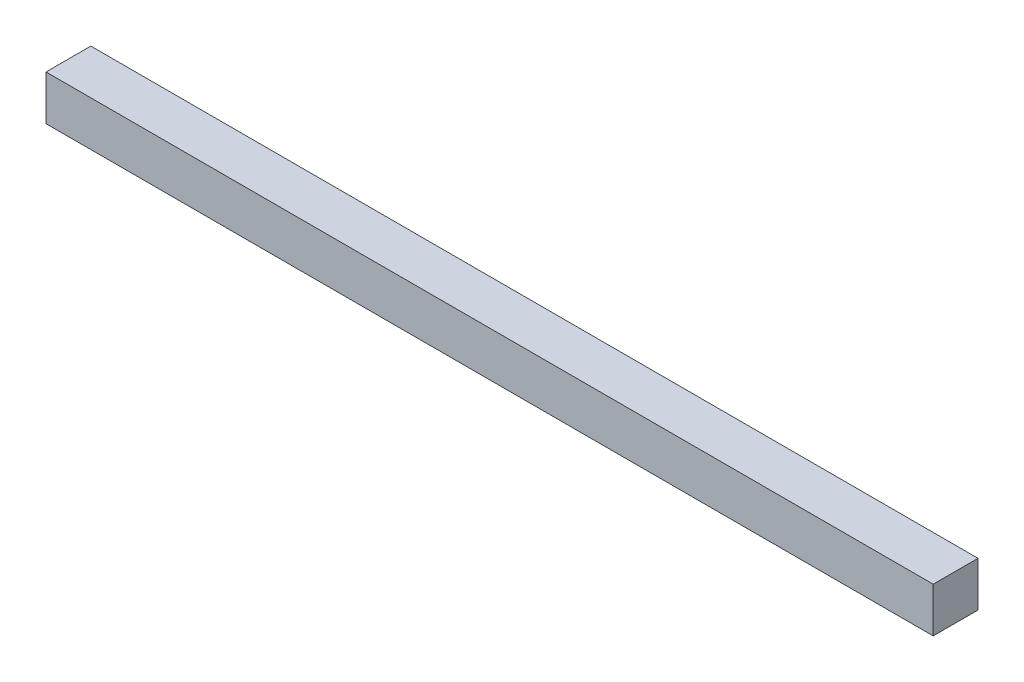
SolidWorks part; units mm, degrees
ref_plane "Front Plane" through (0, 0, 0) normal (0, 0, 1) x (1, 0, 0)
ref_plane "Top Plane" through (0, 0, 0) normal (0, 1, 0) x (1, 0, 0)
ref_plane "Right Plane" through (0, 0, 0) normal (1, 0, 0) x (0, 0, -1)
sketch "Sketch1" plane through (0, 0, 0) normal (0, 0, 1) x (1, 0, 0)
  line L1 (-49.5, -2.5) -> (49.5, -2.5)
  line L2 (-49.5, -2.5) -> (-49.5, 2.5)
  line L3 (-49.5, 2.5) -> (49.5, 2.5)
  line L4 (49.5, -2.5) -> (49.5, 2.5)
  line L5 (-49.5, -2.5) -> (49.5, 2.5) construction
  line L6 (-49.5, 2.5) -> (49.5, -2.5) construction
  point P0 (0, 0)
extrude "Boss-Extrude1" add sketch "Sketch1" along normal blind 5
